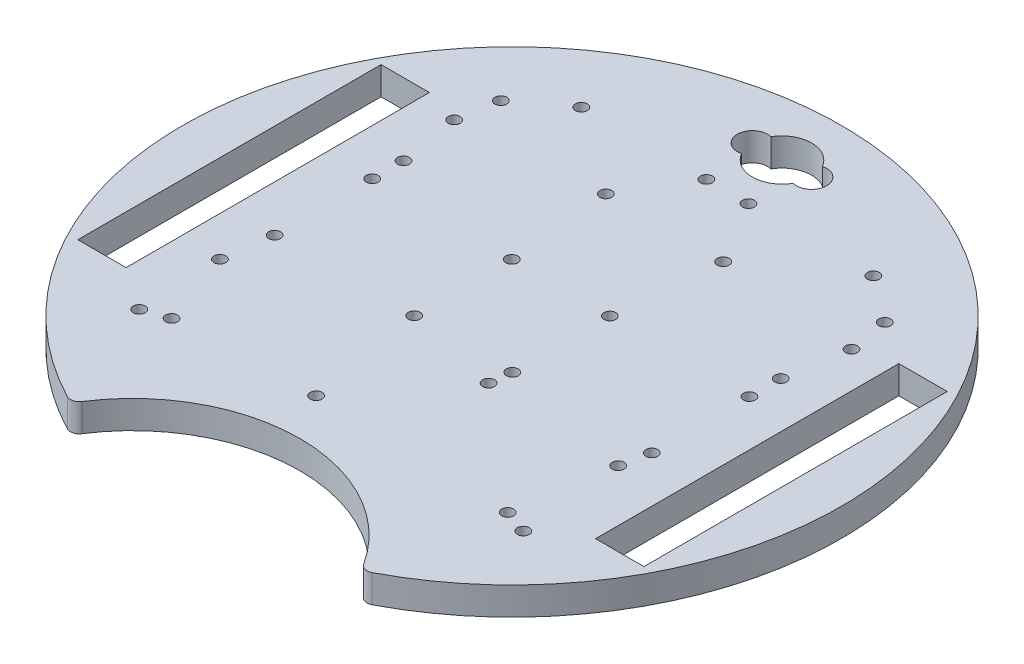
SolidWorks part; units mm, degrees
ref_plane "Front Plane" through (0, 0, 0) normal (0, 0, 1) x (1, 0, 0)
ref_plane "Top Plane" through (0, 0, 0) normal (0, 1, 0) x (1, 0, 0)
ref_plane "Right Plane" through (0, 0, 0) normal (1, 0, 0) x (0, 0, -1)
sketch "Sketch1" plane through (0, 0, 0) normal (0, 1, 0) x (1, 0, 0)
  line L0 (0, 0) -> (-43.685, 41.1293) construction
  line L1 (0, 86.2583) -> (0, -96.8543) construction
  line L3 (-32.9956, -67.352) -> (0, -86.402) construction
  line L4 (32.9956, -67.352) -> (0, -86.402) construction
  line L5 (0, 0) -> (-13.6167, -50.8184) construction
  line L7 (0, 0) -> (-48.2091, 57.4533) construction
  line L8 (-83.3992, 0) -> (107.0959, 0) construction
  line L9 (53.4101, -34.3971) -> (53.4101, 34.6029)
  line L10 (-64.4101, -34.3971) -> (-53.4101, -34.3971)
  line L11 (-64.4101, -34.3971) -> (-64.4101, 34.6029)
  line L12 (-64.4101, 34.6029) -> (-53.4101, 34.6029)
  line L13 (-53.4101, -34.3971) -> (-53.4101, 34.6029)
  line L14 (64.4101, 34.6029) -> (53.4101, 34.6029)
  line L15 (64.4101, -34.3971) -> (64.4101, 34.6029)
  line L16 (64.4101, -34.3971) -> (53.4101, -34.3971)
  line L17 (0, 0) -> (13.6167, -50.8184) construction
  line L19 (0, 0) -> (48.2091, 57.4533) construction
  line L21 (64.9519, -37.5) -> (0, 0) construction
  line L35 (-13.6167, -50.8184) -> (-25.1096, -20.9046) construction
  line L38 (13.6167, -50.8184) -> (24.3327, -22.8079) construction
  line L42 (-58.5537, 0) -> (91.2411, 0) construction
  line L46 (0, 34.6626) -> (0, -51.647) construction
  line L47 (-37.1849, 0) -> (48.113, 0) construction
  line L48 (0, 49.2959) -> (0, -33.0158) construction
  line L54 (8.45, 45.0502) -> (-8.45, 71.1502) construction
  line L55 (8.45, 71.1502) -> (-8.45, 45.0502) construction
  arc A0 (32.9956, -67.352) -> (-32.9956, -67.352) centre (0, 0) ccw
  arc A1 (32.9956, -67.352) -> (-32.9956, -67.352) centre (0, -86.402) ccw
  circle A2 centre (0, 0) radius 74 construction
  circle A3 centre (-42.9101, 18.2083) radius 1.35
  circle A4 centre (42.9101, 18.2083) radius 1.35
  circle A5 centre (-33.218, 49) radius 1.35
  circle A6 centre (-4.782, 49) radius 1.35
  circle A7 centre (4.782, 49) radius 1.35
  circle A8 centre (33.218, 49) radius 1.35
  circle A9 centre (0, 0) radius 60 construction
  circle A19 centre (-42.9101, 11.1) radius 1.35
  circle A20 centre (-42.9101, -11.1) radius 1.35
  circle A21 centre (-11.1601, -11.1) radius 1.35
  circle A22 centre (-11.1601, 11.1) radius 1.35
  circle A23 centre (11.1601, 11.1) radius 1.35
  circle A24 centre (11.1601, -11.1) radius 1.35
  circle A25 centre (42.9101, -11.1) radius 1.35
  circle A26 centre (42.9101, 11.1) radius 1.35
  circle A27 centre (26.9058, -20.9046) radius 12.095 construction
  circle A28 centre (19, 49) radius 12.095 construction
  circle A29 centre (0, 29.7936) radius 12.095 construction
  circle A31 centre (29.9399, 24.6519) radius 12.095 construction
  circle A32 centre (-26.9058, -20.9046) radius 12.095 construction
  circle A33 centre (6.731, 61.4226) radius 1.143
  circle A34 centre (-6.731, 61.4226) radius 1.143
  arc A35 (-5.8539, 64.7449) -> (5.8576, 64.7385) centre (0, 61.4226) cw
  arc A36 (5.8576, 64.7385) -> (5.8576, 58.1067) centre (6.731, 61.4226) cw
  arc A37 (-5.8539, 58.1002) -> (-5.8539, 64.7449) centre (-6.731, 61.4226) cw
  arc A38 (5.8576, 58.1067) -> (-5.8539, 58.1002) centre (0, 61.4226) cw
  circle A39 centre (-29.9399, 24.6519) radius 12.095 construction
  circle A43 centre (-31.8456, 27.1374) radius 12.095 construction
  circle A48 centre (31.8456, 27.1374) radius 12.095 construction
  circle A49 centre (-19, 49) radius 12.095 construction
  circle A50 centre (45.1924, 32.0376) radius 1.35
  circle A51 centre (-45.1924, 32.0376) radius 1.35
  circle A52 centre (13.3469, 34.6938) radius 1.35
  circle A53 centre (-6.5548, -38.0261) radius 1.35
  circle A54 centre (-31.8456, 27.1374) radius 14.218 construction
  circle A55 centre (-13.3469, 34.6938) radius 1.35
  circle A56 centre (10.597, -15.93) radius 1.35
  circle A57 centre (-38.2343, -39.237) radius 1.35
  circle A58 centre (0, 29.7936) radius 14.218 construction
  circle A59 centre (-43.685, -41.1293) radius 1.35
  circle A60 centre (-43.685, 41.1293) radius 1.35
  circle A61 centre (43.685, -41.1293) radius 1.35
  circle A62 centre (31.8456, 27.1374) radius 14.218 construction
  circle A66 centre (-19, 49) radius 14.218 construction
  circle A67 centre (43.685, 41.1293) radius 1.35
  circle A70 centre (19, 49) radius 14.218 construction
  circle A71 centre (-44.3852, -22.0742) radius 1.35
  circle A74 centre (-31.0383, -26.9744) radius 14.218 construction
  circle A78 centre (0, -25.4092) radius 14.218 construction
  circle A80 centre (41.6017, -17.4578) radius 1.35
  circle A81 centre (38.2343, -39.237) radius 1.35
  circle A82 centre (31.0383, -26.9744) radius 14.218 construction
  point P14 (-62.6039, 0)
  point P23 (62.6039, 0)
  point P35 (-31.5178, -45.012)
  point P40 (-46.7211, -26.9744)
  point P45 (-34.6777, 41.3272)
  point P84 (-20.4871, -32.9362)
  point P154 (0, 58.1002)
  dimension "D1" = 150
  dimension "D2" = 76.2
  dimension "D10" = 148
  dimension "D13" = 2.7
  dimension "D14" = 2.7
  dimension "D22" = 2.286
  dimension "D20" = 2.7
  dimension "D8" = 2.7
  dimension "D11" = 2.7
  dimension "D3" = 120
  dimension "D4" = 69
  dimension "D5" = 11
  dimension "D9" = 30
  dimension "D17" = 22.2
  dimension "D19" = 22.2
  dimension "D15" = 10.5
  dimension "D18" = 31.75
  dimension "D23" = 13.462
  dimension "D24" = 16.9
  dimension "D25" = 26.1
  dimension "D6" = 38
  dimension "D7" = 49
  dimension "D12" = 6.726
extrude "Boss-Extrude1" add sketch "Sketch1" along normal blind 6.35
fillet "Fillet1" radius 2 2 edges at (-32.9956, 3.175, 67.352) (32.9956, 3.175, 67.352)
equation "\"D10@Sketch1\"=150-2"
